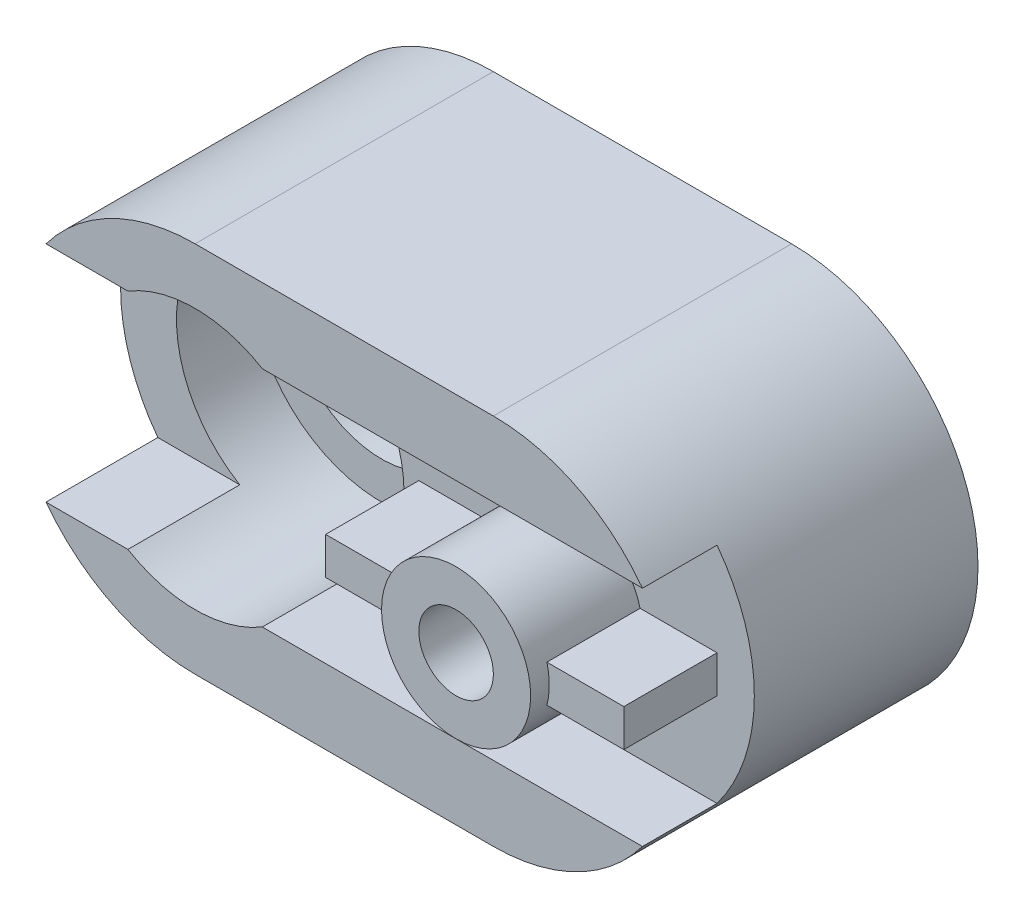
SolidWorks part; units mm, degrees
ref_plane "Front Plane" through (0, 0, 0) normal (0, 0, 1) x (1, 0, 0)
ref_plane "Top Plane" through (0, 0, 0) normal (0, 1, 0) x (1, 0, 0)
ref_plane "Right Plane" through (0, 0, 0) normal (1, 0, 0) x (0, 0, -1)
sketch "Sketch1" plane through (0, 0, 0) normal (0, 0, 1) x (1, 0, 0)
  line L1 (0, 0) -> (180, 0)
  line L2 (0, 0) -> (0, 100)
  line L3 (0, 100) -> (180, 100)
  line L4 (180, 0) -> (180, 100)
  arc A0 (50, 100) -> (50, 0) centre (50, 50) ccw
  arc A1 (130, 100) -> (130, 0) centre (130, 50) cw
  dimension "D7" = 50
  dimension "D10" = 50
  dimension "D1" = 180
  dimension "D2" = 100
  dimension "D3" = 50
  dimension "D4" = 50
  dimension "D5" = 50
  dimension "D6" = 50
  dimension "D8" = 50
  dimension "D9" = 50
extrude "Boss-Extrude1" add sketch "Sketch1" along normal blind 80 contours A1 L3 A0 L1
sketch "Sketch2" plane through (0, 0, 0) normal (1, 0, 0) x (0, 0, -1)
  line L0 (-80, 100) -> (-80, 0) construction
  line L1 (-80, 80) -> (-60, 80)
  line L2 (-80, 80) -> (-80, 70)
  line L3 (-80, 70) -> (-60, 70)
  line L4 (-60, 80) -> (-60, 70)
  line L5 (-80, 100) -> (0, 100) construction
  line L6 (-80, 0) -> (0, 0) construction
  line L7 (-80, 30) -> (-60, 30)
  line L8 (-80, 30) -> (-80, 20)
  line L9 (-80, 20) -> (-60, 20)
  line L10 (-60, 30) -> (-60, 20)
  dimension "D1" = 20
  dimension "D2" = 10
  dimension "D3" = 20
  dimension "D4" = 10
  dimension "D5" = 20
  dimension "D6" = 20
extrude "Cut-Extrude1" cut sketch "Sketch2" along normal blind 209
sketch "Sketch3" plane through (0, 0, 80) normal (0, 0, 1) x (1, 0, 0)
  line L0 (50, 0) -> (130, 0) construction
  circle A0 centre (130, 50) radius 10
  arc A1 (175.8258, 30) -> (175.8258, 70) centre (130, 50) ccw construction
  point P2 (180, 50)
  dimension "D1" = 20
  dimension "D2" = 50
  dimension "D3" = 50
extrude "Cut-Extrude2" cut sketch "Sketch3" against normal blind 40
sketch "Sketch4" plane through (0, 0, 80) normal (0, 0, 1) x (1, 0, 0)
  circle A0 centre (130, 50) radius 10
  circle A1 centre (130, 50) radius 20
  dimension "D1" = 20
  dimension "D2" = 40
extrude "Boss-Extrude2" add sketch "Sketch4" along normal blind 10
sketch "Sketch7" plane through (0, 0, 90) normal (0, 0, 1) x (1, 0, 0)
  point P0 (130, 50)
hole_wizard "Ø20.0mm Dowel Hole1" positions "3DSketch3" profile "Sketch8" hole size "Ø20.0" standard "ISO"
sketch3d "3DSketch3"
  point P0 (130, 50, 90)
sketch "Sketch8" plane through (130, 50, 90) normal (1, 0, 0) x (0, -1, 0)
  line L0 (0, 0) -> (0, 56.0086)
  line L1 (0, 56.0086) -> (10, 50)
  line L2 (10, 50) -> (10, 0)
  line L5 (10, 0) -> (0, 0)
  line L10 (0, 56.0086) -> (-10, 50) construction
  line L11 (0, -6.35) -> (0, 107.95) construction
  dimension "Hole Dia." = 20
  dimension "Hole Depth" = 50
  dimension "Drill Angle" = 118
sketch "Sketch9" plane through (0, 0, 80) normal (0, 0, 1) x (1, 0, 0)
  line L0 (4.1742, 30) -> (130, 30) construction
  line L1 (130, 70) -> (4.1742, 70)
  line L2 (130, 30) -> (4.1742, 30)
  arc A0 (130, 70) -> (130, 30) centre (130, 50) ccw
  arc A1 (4.1742, 70) -> (4.1742, 30) centre (50, 50) ccw
  arc A2 (4.1742, 70) -> (4.1742, 30) centre (50, 50) ccw construction
extrude "Cut-Extrude3" cut sketch "Sketch9" against normal blind 20
sketch "Sketch10" plane through (0, 0, 60) normal (0, 0, 1) x (1, 0, 0)
  line L0 (50, 0) -> (130, 0) construction
  circle A0 centre (50, 50) radius 10
  arc A1 (50, 100) -> (50, 0) centre (50, 50) ccw construction
  point P4 (0, 50)
  dimension "D1" = 20
  dimension "D2" = 50
  dimension "D3" = 50
extrude "Cut-Extrude4" cut sketch "Sketch10" against normal blind 74
sketch "Sketch11" plane through (0, 0, 60) normal (0, 0, 1) x (1, 0, 0)
  circle A0 centre (50, 50) radius 10
  circle A1 centre (50, 50) radius 25
  dimension "D1" = 20
  dimension "D2" = 50
extrude "Cut-Extrude5" cut sketch "Sketch11" against normal blind 40
sketch "Sketch12" plane through (0, 0, 60) normal (0, 0, 1) x (1, 0, 0)
  line L0 (170, 20) -> (10, 20) construction
  line L1 (10, 80) -> (70, 80)
  line L2 (170, 80) -> (10, 80) construction
  line L3 (10, 20) -> (70, 20)
  arc A0 (10, 80) -> (10, 20) centre (50, 50) ccw
  arc A1 (70, 80) -> (70, 20) centre (50, 50) cw
  circle M1 centre (50, 50) radius 25
  line M2 (170, 80) -> (10, 80)
  arc M3 (10, 80) -> (10, 20) centre (50, 50) ccw
  line M4 (10, 20) -> (170, 20)
  dimension "D1" = 60
  dimension "D2" = 60
extrude "Cut-Extrude6" cut sketch "Sketch12" against normal blind 10 contours A1 M2 M3 M4 M1
sketch "Sketch14" plane through (0, 0, 60) normal (0, 0, 1) x (1, 0, 0)
  circle A0 centre (50, 50) radius 35
  circle A1 centre (50, 50) radius 25
  dimension "D1" = 70
  dimension "D2" = 50
extrude "Cut-Extrude7" cut sketch "Sketch14" against normal blind 30
sketch "Sketch15" plane through (0, 0, 80) normal (0, 0, 1) x (1, 0, 0)
  circle A0 centre (50, 50) radius 35
  dimension "D1" = 70
extrude "Cut-Extrude8" cut sketch "Sketch15" against normal blind 30
sketch "Sketch16" plane through (0, 0, 80) normal (0, 0, 1) x (1, 0, 0)
  line L0 (130, 70) -> (175.8258, 70)
  line L1 (130, 30) -> (175.8258, 30)
  arc A0 (130, 70) -> (130, 30) centre (130, 50) cw
  arc A1 (175.8258, 70) -> (175.8258, 30) centre (130, 50) cw
  arc A2 (175.8258, 30) -> (175.8258, 70) centre (130, 50) ccw construction
extrude "Cut-Extrude9" cut sketch "Sketch16" against normal blind 20
sketch "Sketch17" plane through (0, 0, 60) normal (0, 0, 1) x (1, 0, 0)
  line L1 (110, 50) -> (90, 50)
  line L2 (110, 50) -> (110, 45)
  line L3 (110, 45) -> (90, 45)
  line L4 (90, 50) -> (90, 45)
  line L5 (150, 50) -> (170, 50)
  line L6 (150, 50) -> (150, 45)
  line L7 (150, 45) -> (170, 45)
  line L8 (170, 50) -> (170, 45)
  line L9 (50, 0) -> (130, 0) construction
  line L10 (110, 45) -> (110.6351, 45)
  line L11 (150, 45) -> (149.3649, 45)
  circle A0 centre (130, 50) radius 20 construction
  arc A1 (110, 50) -> (110.6351, 45) centre (130, 50) ccw
  arc A2 (150, 50) -> (149.3649, 45) centre (130, 50) cw
  circle M1 centre (130, 50) radius 20
  dimension "D1" = 20
  dimension "D2" = 5
  dimension "D3" = 5
  dimension "D4" = 20
  dimension "D5" = 45
  dimension "D6" = 45
extrude "Boss-Extrude3" add sketch "Sketch17" along normal blind 25 contours L11 L6 M1 | L8 L5 L6 L7 | L2 L10 M1 | L1 L4 L3 L2
sketch "Sketch18" plane through (0, 0, 85) normal (0, 0, 1) x (1, 0, 0)
  line L0 (110, 55) -> (110.6351, 55)
  line L1 (90, 50) -> (110, 50)
  line L2 (90, 50) -> (90, 55)
  line L3 (90, 55) -> (110, 55)
  line L4 (110, 50) -> (110, 55)
  circle A0 centre (130, 50) radius 20 construction
  arc A1 (110.6351, 55) -> (110, 50) centre (130, 50) ccw
  line M2 (110, 50) -> (90, 50)
  dimension "D1" = 5
  dimension "D2" = 20
extrude "Boss-Extrude4" add sketch "Sketch18" against normal blind 25 contours A1 L0 L4 | L4 L3 L2 M2
sketch "Sketch19" plane through (0, 0, 85) normal (0, 0, 1) x (1, 0, 0)
  line L0 (150, 55) -> (149.3649, 55)
  line L1 (170, 50) -> (150, 50)
  line L2 (170, 50) -> (170, 55)
  line L3 (170, 55) -> (150, 55)
  line L4 (150, 50) -> (150, 55)
  circle A0 centre (130, 50) radius 20 construction
  arc A1 (149.3649, 55) -> (150, 50) centre (130, 50) cw
  line M3 (170, 50) -> (150, 50)
  dimension "D1" = 5
  dimension "D2" = 20
extrude "Boss-Extrude5" add sketch "Sketch19" against normal blind 25 contours L0 A1 L4 | L4 L2 L3 M3
